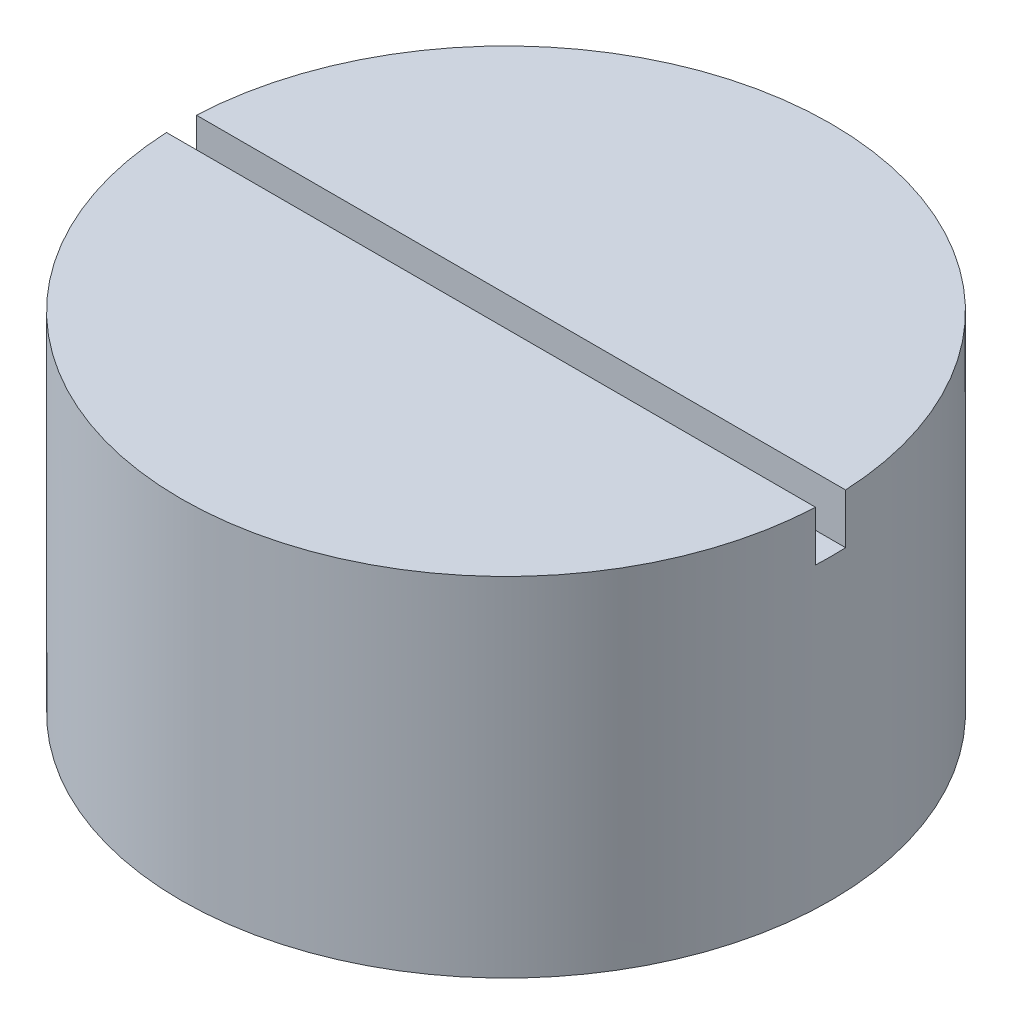
SolidWorks part; units mm, degrees
ref_plane "Front Plane" through (0, 0, 0) normal (0, 0, 1) x (1, 0, 0)
ref_plane "Top Plane" through (0, 0, 0) normal (0, 1, 0) x (1, 0, 0)
ref_plane "Right Plane" through (0, 0, 0) normal (1, 0, 0) x (0, 0, -1)
sketch "Sketch1" plane through (0, 0, 0) normal (0, 1, 0) x (1, 0, 0)
  circle A0 centre (0, 0) radius 32.5
  dimension "D1" = 65
extrude "Boss-Extrude1" add sketch "Sketch1" along normal blind 34.793
sketch "Sketch4" plane through (0, 34.793, 0) normal (0, 1, 0) x (1, 0, 0)
  line L0 (-32.5, 0) -> (32.5, 0) construction
  line L2 (-33.1901, -1.5) -> (33.1901, -1.5)
  line L3 (-33.1901, -1.5) -> (-33.1901, 1.5)
  line L4 (-33.1901, 1.5) -> (33.1901, 1.5)
  line L5 (33.1901, -1.5) -> (33.1901, 1.5)
  line L6 (-33.1901, -1.5) -> (33.1901, 1.5) construction
  line L7 (-33.1901, 1.5) -> (33.1901, -1.5) construction
  circle A0 centre (0, 0) radius 32.5 construction
  point P5 (0, 0)
  dimension "D1" = 3
extrude "Cut-Extrude1" cut sketch "Sketch4" against normal blind 5
sketch "Sketch5" plane through (0, 0, 0) normal (0, -1, 0) x (1, 0, 0)
  circle A0 centre (0, 0) radius 6
  circle A1 centre (0, 0) radius 8
  dimension "D1" = 12
  dimension "D2" = 16
extrude "Cut-Extrude2" cut sketch "Sketch5" against normal blind 2
